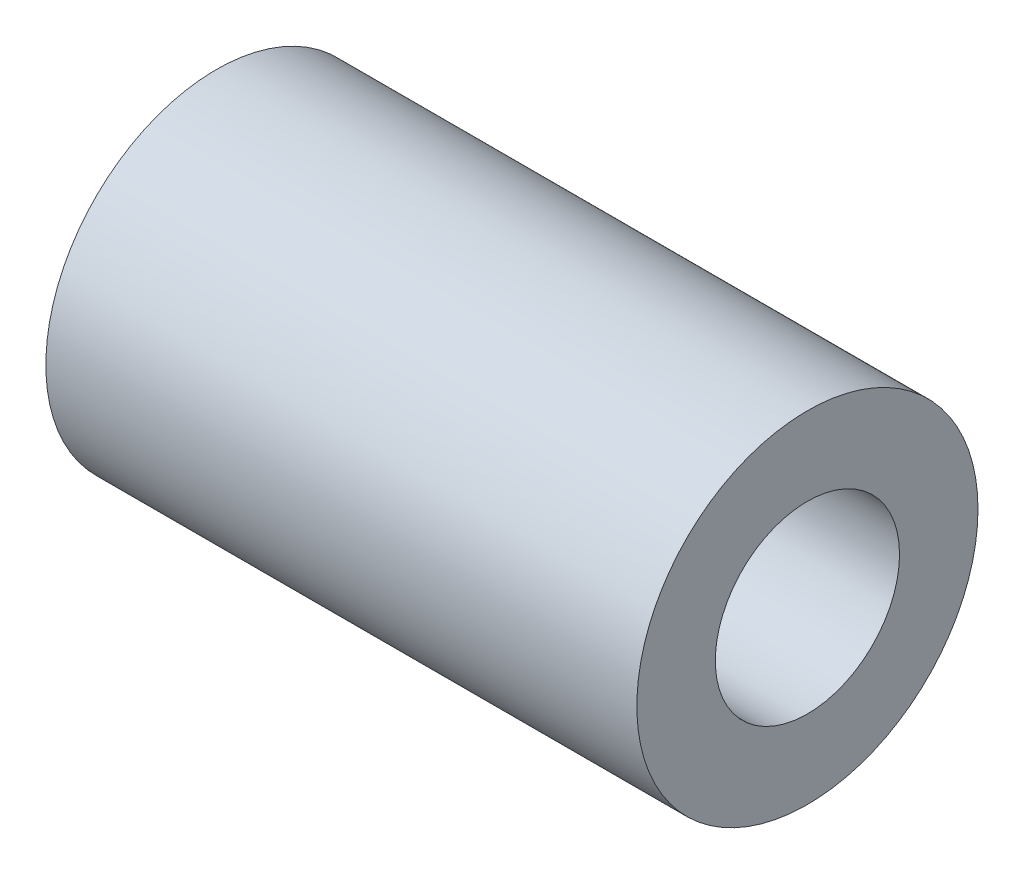
SolidWorks part; units mm, degrees
ref_plane "Plan de face" through (0, 0, 0) normal (0, 0, 1) x (1, 0, 0)
ref_plane "Plan de dessus" through (0, 0, 0) normal (0, 1, 0) x (1, 0, 0)
ref_plane "Plan de droite" through (0, 0, 0) normal (1, 0, 0) x (0, 0, -1)
sketch "Esquisse1" plane through (0, 0, 0) normal (1, 0, 0) x (0, 0, -1)
  circle A0 centre (0, 0) radius 3.429
  circle A1 centre (0, 0) radius 6.35
  dimension "D1" = 6.858
  dimension "D2" = 12.7
extrude "Boss.-Extru.1" add sketch "Esquisse1" against normal blind 22
equation "\"D1@Boss.-Extru.1\"=22mm"
